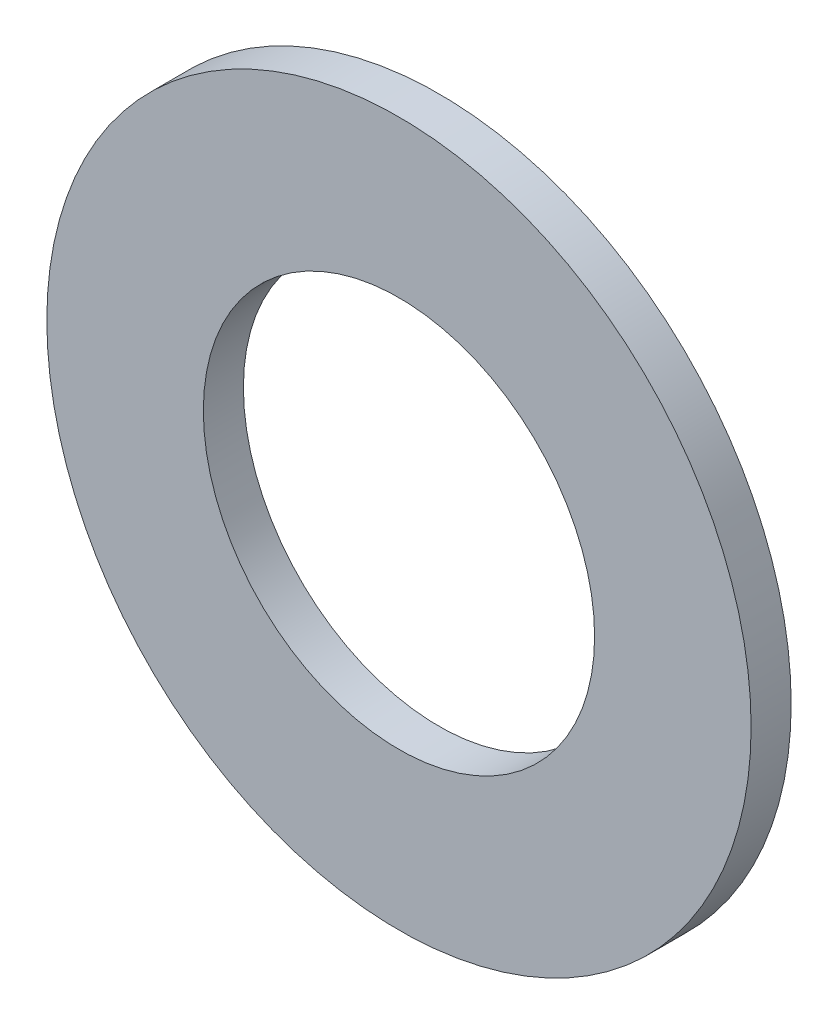
SolidWorks part; units mm, degrees
ref_plane "Top" through (0, 0, 0) normal (0, 0, 1) x (1, 0, 0)
ref_plane "Right" through (0, 0, 0) normal (0, 1, 0) x (1, 0, 0)
ref_plane "Front" through (0, 0, 0) normal (1, 0, 0) x (0, 0, -1)
sketch "Sketch1" plane through (0, 0, 0) normal (0, 0, 1) x (1, 0, 0)
  circle A0 centre (0, 0) radius 7.1438
  circle A1 centre (0, 0) radius 3.9688
  dimension "D1" = 7.9375
  dimension "D2" = 14.2875
extrude "Boss-Extrude1" add sketch "Sketch1" along normal blind 0.8128
move or copy body "Body-Move/Copy2" [suppressed] bodies to move or copy 101
move or copy body "Body-Move/Copy3" [suppressed] bodies to move or copy 101
move or copy body "Body-Move/Copy1" [suppressed] bodies to move or copy 101
